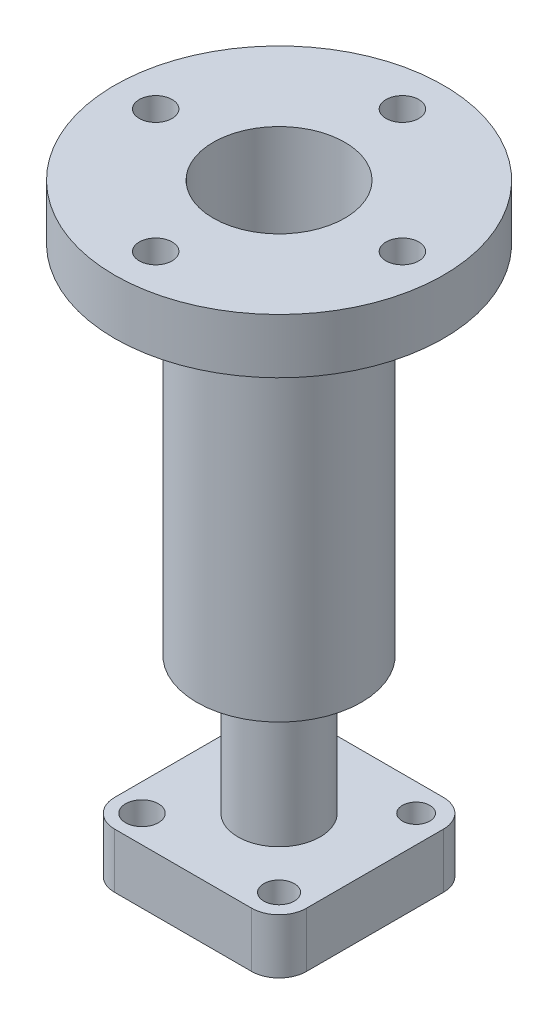
SolidWorks part; units mm, degrees
ref_plane "Front Plane" through (0, 0, 0) normal (0, 0, 1) x (1, 0, 0)
ref_plane "Top Plane" through (0, 0, 0) normal (0, 1, 0) x (1, 0, 0)
ref_plane "Right Plane" through (0, 0, 0) normal (1, 0, 0) x (0, 0, -1)
sketch "Sketch1" plane through (0, 0, 0) normal (0, 0, 1) x (1, 0, 0)
  line L0 (0, 218.0832) -> (0, -221.6998) construction
  line L1 (-420.2532, 0) -> (371.0669, 0) construction
  line L2 (0, 0) -> (15, 0)
  line L3 (15, 0) -> (15, 50)
  line L4 (15, 50) -> (30, 50)
  line L5 (30, 50) -> (30, 180)
  line L6 (30, 180) -> (60, 180)
  line L7 (60, 180) -> (60, 200)
  line L8 (60, 200) -> (0, 200)
  line L9 (0, 200) -> (0, 0)
  dimension "D1" = 200
  dimension "D2" = 60
  dimension "D3" = 20
  dimension "D4" = 30
  dimension "D5" = 15
  dimension "D6" = 50
revolve "Revolve1" add sketch "Sketch1" angle 360 about L0
sketch "Sketch2" plane through (0, 200, 0) normal (0, 1, 0) x (1, 0, 0)
  circle A0 centre (0, 0) radius 45 construction
  circle A1 centre (0, 45) radius 6
  dimension "D1" = 90
  dimension "D2" = 12
extrude "Cut-Extrude1" cut sketch "Sketch2" against normal through all
pattern_circular "CirPattern1" count 4 over 360 about axis through (0, 0, 0) along (0, 1, 0) of "Cut-Extrude1"
sketch "Sketch3" plane through (0, 200, 0) normal (0, 1, 0) x (1, 0, 0)
  circle A0 centre (0, 0) radius 24
  dimension "D1" = 48
extrude "Cut-Extrude2" cut sketch "Sketch3" against normal blind 144 contours A0
sketch "Sketch4" plane through (0, 0, 0) normal (0, -1, 0) x (1, 0, 0)
  line L1 (-25, 35) -> (25, 35)
  line L2 (-35, 25) -> (-35, -25)
  line L3 (-25, -35) -> (25, -35)
  line L4 (35, 25) -> (35, -25)
  line L5 (-35, 35) -> (35, -35) construction
  line L6 (-35, -35) -> (35, 35) construction
  arc A0 (35, 25) -> (25, 35) centre (25, 25) ccw
  arc A1 (25, -35) -> (35, -25) centre (25, -25) ccw
  arc A2 (-25, -35) -> (-35, -25) centre (-25, -25) cw
  arc A3 (-35, 25) -> (-25, 35) centre (-25, 25) cw
  point P0 (0, 0)
  dimension "D3" = 10
  dimension "D1" = 70
  dimension "D2" = 70
extrude "Boss-Extrude2" add sketch "Sketch4" along normal blind 20
sketch "Sketch8" plane through (0, -20, 0) normal (0, -1, 0) x (1, 0, 0)
  line L0 (0, 71.9243) -> (0, -75.0778) construction
  line L1 (-87.0854, 0) -> (109.8877, 0) construction
  circle A0 centre (25, 25) radius 6
  circle A1 centre (25, -25) radius 6
  circle A2 centre (-25, -25) radius 6
  circle A3 centre (-25, 25) radius 6
  dimension "D1" = 12
extrude "Cut-Extrude3" cut sketch "Sketch8" against normal up to next contours A3
sketch "Sketch10" plane through (0, -20, 0) normal (0, -1, 0) x (-1, 0, 0)
  circle A0 centre (-25, -25) radius 5.552
  dimension "D1" = 10
extrude "Cut-Extrude4" cut sketch "Sketch10" against normal up to next
sketch "Sketch11" plane through (0, -20, 0) normal (0, -1, 0) x (-1, 0, 0)
  line L0 (25, 35) -> (-25, 35) construction
  line L1 (-35, 25) -> (-35, -25) construction
  circle A0 centre (-25, 25) radius 5
  dimension "D1" = 10
  dimension "D2" = 10
  dimension "D3" = 10
extrude "Cut-Extrude5" cut sketch "Sketch11" against normal up to next
sketch "Sketch12" plane through (0, -20, 0) normal (0, -1, 0) x (1, 0, 0)
  circle A0 centre (-25, -25) radius 5
  dimension "D1" = 10
extrude "Cut-Extrude6" cut sketch "Sketch12" against normal up to next and the other way through all
sketch "Sketch6" plane through (0, -20, 0) normal (0, -1, 0) x (1, 0, 0)
  line L0 (0, 65.0942) -> (0, -69.9384) construction
